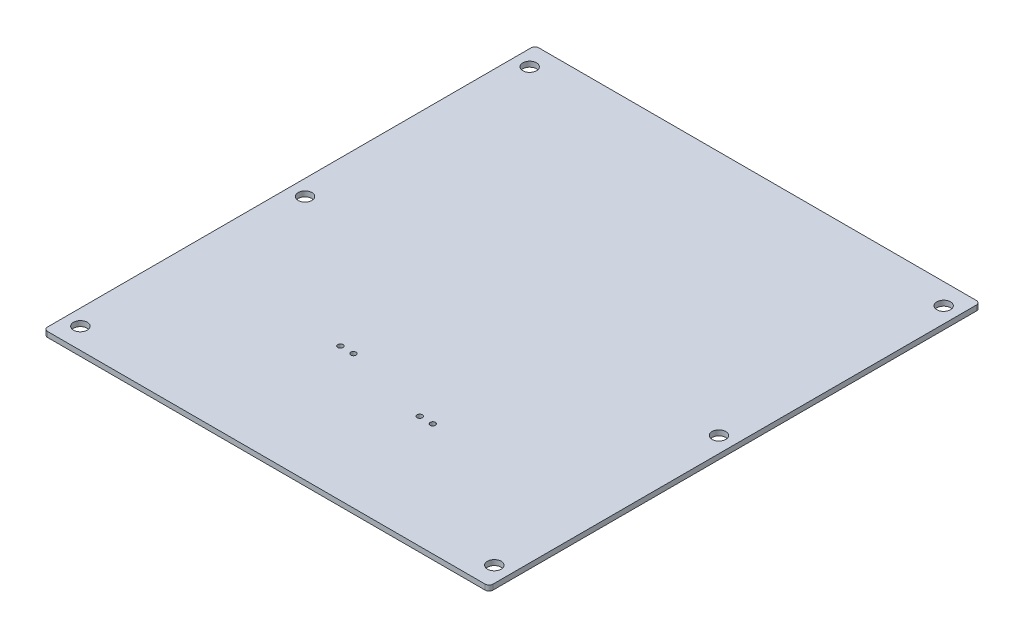
SolidWorks part; units mm, degrees
material "1060 Alloy"
ref_plane "Front Plane" through (0, 0, 0) normal (0, 0, 1) x (1, 0, 0)
ref_plane "Top Plane" through (0, 0, 0) normal (0, 1, 0) x (1, 0, 0)
ref_plane "Right Plane" through (0, 0, 0) normal (1, 0, 0) x (0, 0, -1)
sketch "Sketch1" plane through (0, 0, 0) normal (0, 1, 0) x (1, 0, 0)
  line L52 (316.226, 107.292) -> (316.226, -261.708)
  line L53 (319.226, -264.708) -> (653.226, -264.708)
  line L54 (656.226, -261.708) -> (656.226, 107.292)
  line L55 (653.226, 110.292) -> (319.226, 110.292)
  line L56 (377.026, -162.6142) -> (581.1343, -162.6142) construction
  line L59 (460.619, -168.4997) -> (460.619, -150.4874) construction
  line L60 (460.619, -150.4874) -> (517.119, -150.4874) construction
  line L61 (517.119, -187.6012) -> (517.119, -150.4874) construction
  line L62 (460.619, -168.4997) -> (517.119, -150.4874) construction
  line L63 (460.619, -150.4874) -> (517.119, -187.6012) construction
  arc A0 (319.226, 110.292) -> (316.226, 107.292) centre (319.226, 107.292) ccw
  arc A1 (316.226, -261.708) -> (319.226, -264.708) centre (319.226, -261.708) ccw
  arc A8 (653.226, -264.708) -> (656.226, -261.708) centre (653.226, -261.708) ccw
  arc A9 (656.226, 107.292) -> (653.226, 110.292) centre (653.226, 107.292) ccw
  circle A12 centre (450.619, -162.6142) radius 2
  circle A13 centre (440.619, -162.6142) radius 2
  circle A14 centre (517.3302, -178.7374) radius 2
  circle A15 centre (644.226, -77.208) radius 5.25
  circle A16 centre (328.226, -77.208) radius 5.25
  circle A17 centre (644.226, 94.292) radius 5.25
  circle A18 centre (328.226, 94.292) radius 5.25
  circle A19 centre (328.226, -248.708) radius 5.25
  circle A20 centre (644.226, -248.708) radius 5.25
  circle A21 centre (527.3302, -178.7374) radius 2
  point P81 (479.0802, -162.6142)
  dimension "D20" = 10
  dimension "D21" = 10
  dimension "D27" = 56.5
extrude "Boss-Extrude1" add sketch "Sketch1" along normal blind 4
